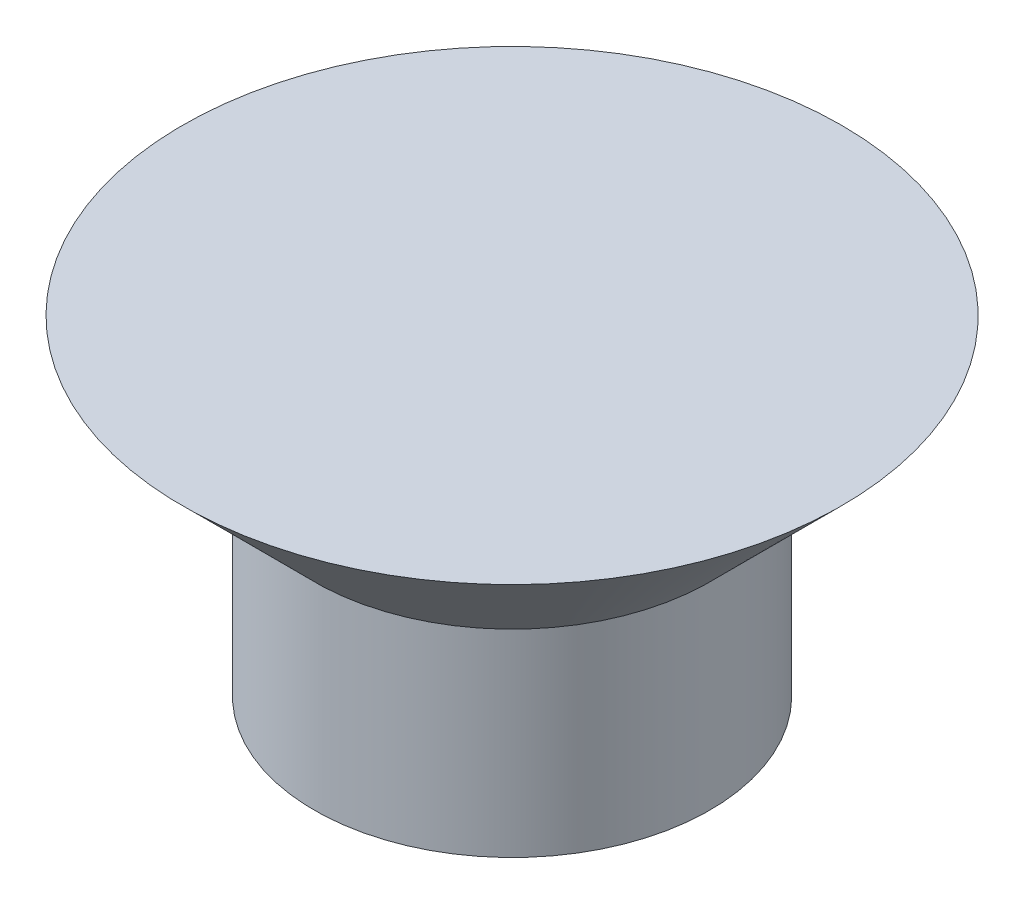
SolidWorks part; units mm, degrees
ref_plane "Front Plane" through (0, 0, 0) normal (0, 0, 1) x (1, 0, 0)
ref_plane "Top Plane" through (0, 0, 0) normal (0, 1, 0) x (1, 0, 0)
ref_plane "Right Plane" through (0, 0, 0) normal (1, 0, 0) x (0, 0, -1)
sketch "Sketch1" plane through (0, 0, 0) normal (0, 0, 1) x (1, 0, 0)
  line L0 (0, 0) -> (0, 2.5)
  line L1 (0, 2.5) -> (2.5, 2.5)
  line L2 (2.5, 2.5) -> (1.5, 1.5)
  line L3 (1.5, 1.5) -> (1.5, 0)
  line L4 (1.5, 0) -> (0, 0)
  dimension "D1" = 2.5
  dimension "D2" = 2.5
  dimension "D3" = 1.5
  dimension "D4" = 1.5
revolve "Revolve1" add sketch "Sketch1" angle 360 about L0
sketch "Orientation Sketch" plane through (0, 2.5, 0) normal (0, 1, 0) x (1, 0, 0)
  circle A0 centre (0, 0) radius 2.5 construction
  circle A1 centre (0, 0) radius 2.5
  point P3 (0, 0)
other "FormTool1"
